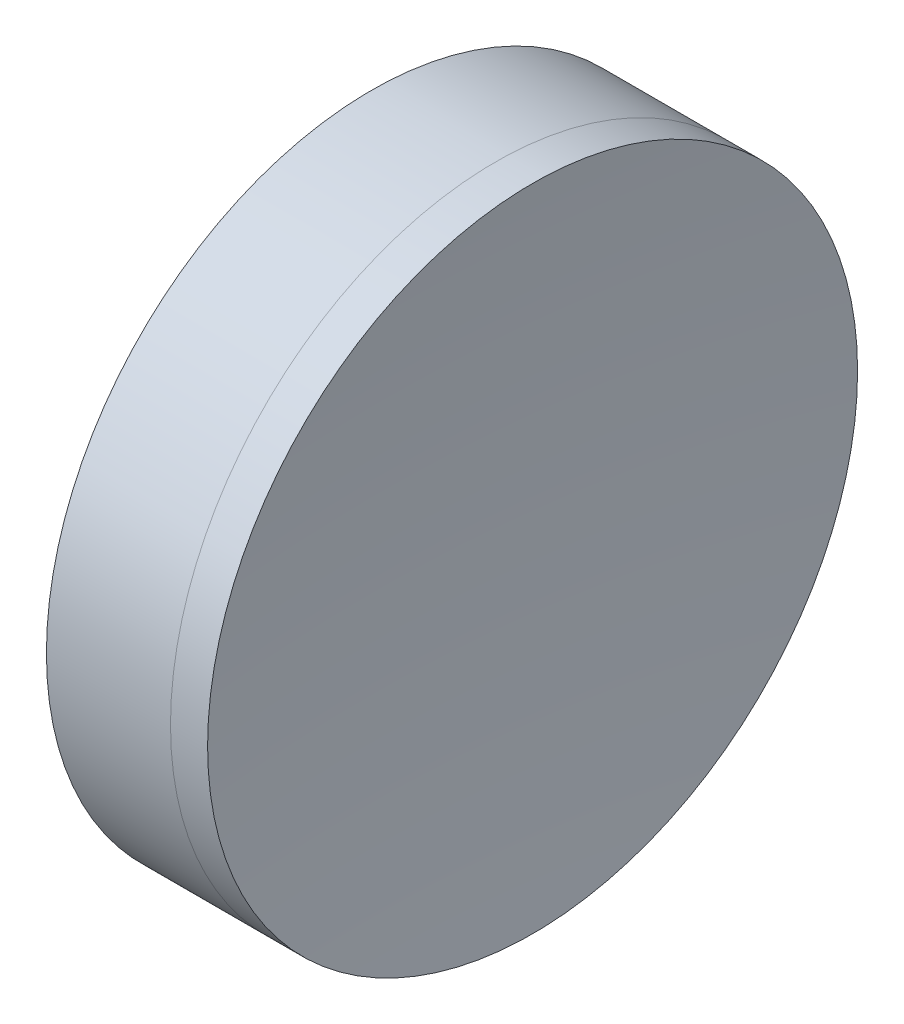
SolidWorks part; units mm, degrees
ref_plane "前视基准面" through (0, 0, 0) normal (0, 0, 1) x (1, 0, 0)
ref_plane "上视基准面" through (0, 0, 0) normal (0, 1, 0) x (1, 0, 0)
ref_plane "右视基准面" through (0, 0, 0) normal (1, 0, 0) x (0, 0, -1)
sketch "草图1" plane through (0, 0, 0) normal (0, 1, 0) x (1, 0, 0)
  line L0 (-0.8161, 0) -> (309.1817, 0) construction
  line L1 (243.5932, 20) -> (251.2286, 20)
  line L4 (243.5932, -20) -> (251.2286, -20)
  arc A0 (243.5932, -20) -> (243.5932, 20) centre (154.1828, 0) ccw
  arc A1 (251.2286, 20) -> (251.2286, -20) centre (318.1228, 0) ccw
  point P6 (245.8028, 0)
  point P8 (248.3028, 0)
  dimension "D3" = 20
  dimension "D4" = 2.5
  dimension "D1" = 91.62
  dimension "D5" = 69.82
  dimension "D2" = 20
revolve "旋转1" add sketch "草图1" angle 360 about L0
sketch "草图2" plane through (0, 0, 0) normal (0, 1, 0) x (1, 0, 0)
  line L2 (243.5932, 0) -> (272.9951, 0) construction
  line L3 (243.5932, -20) -> (243.5932, 20) construction
  line L6 (251.2286, 20) -> (253.512, 20)
  line L7 (251.2286, -20) -> (253.512, -20)
  arc A2 (251.2286, 20) -> (251.2286, -20) centre (318.1228, 0) ccw construction
  arc A3 (251.2286, 20) -> (251.2286, -20) centre (318.1228, 0) ccw
  arc A4 (253.512, 20) -> (253.512, -20) centre (461.5528, 0) ccw
  point P8 (248.3028, 0)
  point P9 (252.5528, 0)
  dimension "D1" = 4.25
  dimension "D2" = 209
revolve "旋转3" add sketch "草图2" angle 360 about L2
